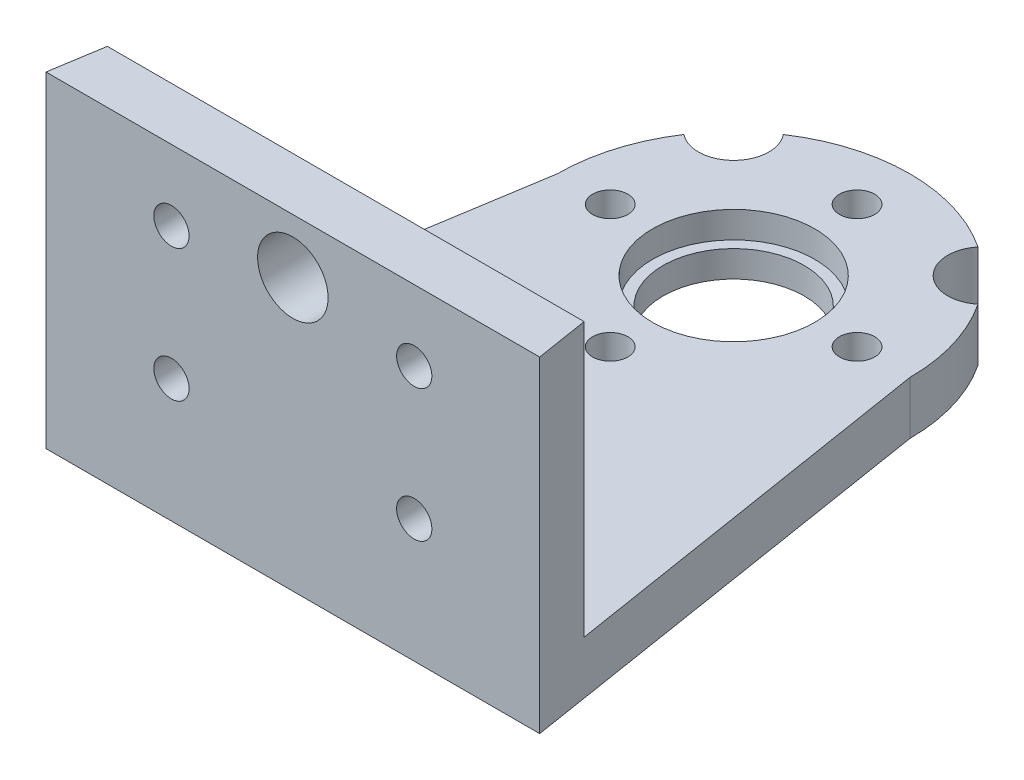
SolidWorks part; units mm, degrees
material "Custom Plastic"
ref_plane "Front Plane" through (0, 0, 0) normal (0, 0, 1) x (1, 0, 0)
ref_plane "Top Plane" through (0, 0, 0) normal (0, 1, 0) x (1, 0, 0)
ref_plane "Right Plane" through (0, 0, 0) normal (1, 0, 0) x (0, 0, -1)
sketch "Sketch1" plane through (0, 0, 0) normal (0, 1, 0) x (1, 0, 0)
  line L0 (-10, 0) -> (-14, -25)
  line L1 (10, 0) -> (14, -25)
  line L2 (0, 17.2103) -> (0, -39.4896) construction
  line L3 (-14, -25) -> (14, -25)
  arc A0 (-10, 0) -> (10, 0) centre (0, 0) cw
  dimension "D1" = 10
  dimension "D2" = 25
  dimension "D3" = 14
extrude "Boss-Extrude1" add sketch "Sketch1" along normal blind 3
sketch "Sketch2" plane through (0, 3, 0) normal (0, 1, 0) x (1, 0, 0)
  line L0 (-21.4034, 0) -> (30.5216, 0) construction
  circle A0 centre (0, 0) radius 4
  dimension "D1" = 8
extrude "Cut-Extrude1" cut sketch "Sketch2" against normal blind 13
sketch "Sketch4" plane through (0, 3, 0) normal (0, 1, 0) x (1, 0, 0)
  line L0 (0, 11.5358) -> (0, -14.2328) construction
  circle A0 centre (0, -7) radius 1
  circle A1 centre (-7, 0) radius 1
  circle A2 centre (0, 7) radius 1
  circle A3 centre (7, 0) radius 1
  point P0 (0, -7)
  point P15 (0, 0)
  dimension "D2" = 2
  dimension "D1" = 7
  dimension "D3" = 4
extrude "Cut-Extrude3" cut sketch "Sketch4" against normal up to vertex (3 mm away) up to point (0, 0, 0)
sketch "Sketch5" plane through (0, 3, 0) normal (0, 1, 0) x (1, 0, 0)
  line L0 (-13.52, -22) -> (13.52, -22)
  line L1 (-10, 0) -> (-14, -25) construction
  line L2 (14, -25) -> (10, 0) construction
  line L3 (-13.52, -22) -> (-14, -25)
  line L4 (-14, -25) -> (14, -25)
  line L5 (14, -25) -> (13.52, -22)
  dimension "D1" = 3
extrude "Boss-Extrude2" add sketch "Sketch5" along normal blind 15.5
sketch "Sketch6" plane through (0, 3, 0) normal (0, 1, 0) x (1, 0, 0)
  circle A0 centre (0, 0) radius 4.6
  dimension "D1" = 9.2
extrude "Cut-Extrude4" cut sketch "Sketch6" against normal blind 1.5
sketch "Sketch7" plane through (0, 3, 0) normal (0, 1, 0) x (1, 0, 0)
  line L0 (0, 12.0905) -> (0, -12.7025) construction
  line L1 (-13.0501, 13.0501) -> (0, 0) construction
  circle A0 centre (-7.0711, 7.0711) radius 2
  arc A1 (10, 0) -> (-10, 0) centre (0, 0) ccw construction
  circle A2 centre (7.0711, 7.0711) radius 2
  dimension "D1" = 4
extrude "Cut-Extrude5" cut sketch "Sketch7" against normal blind 10
sketch "Sketch8" plane through (0, 0, 22) normal (0, 0, -1) x (-1, 0, 0)
  line L0 (-13.52, 3) -> (13.52, 3) construction
  line L1 (-13.52, 18.5) -> (-13.52, 3) construction
  circle A0 centre (6.885, 7) radius 1
  circle A1 centre (-6.885, 7) radius 1
  circle A2 centre (6.885, 14.5) radius 1
  circle A3 centre (-6.885, 14.5) radius 1
  dimension "D1" = 2
  dimension "D2" = 2
  dimension "D3" = 13.77
  dimension "D4" = 4
  dimension "D6" = 6.635
  dimension "D5" = 2
extrude "Cut-Extrude6" cut sketch "Sketch8" against normal blind 10
sketch "Sketch9" plane through (0, 0, 22) normal (0, 0, -1) x (-1, 0, 0)
  circle A2 centre (0, 15.4) radius 2
  dimension "D1" = 4
extrude "Cut-Extrude7" cut sketch "Sketch9" against normal blind 10
